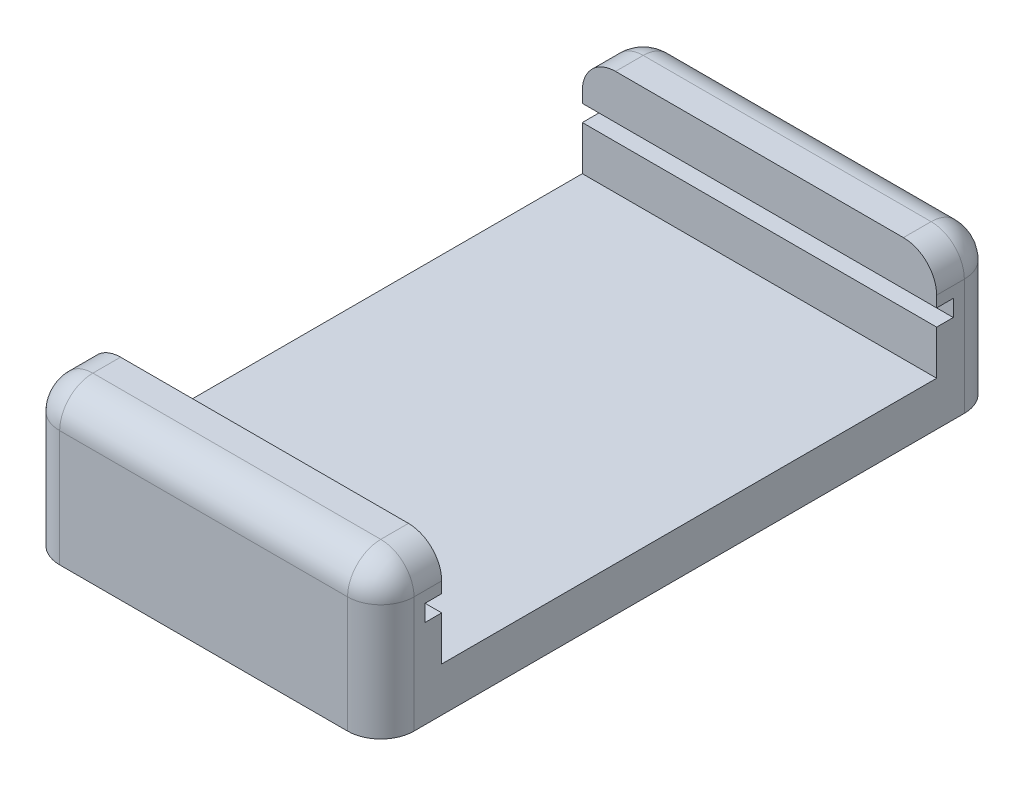
SolidWorks part; units mm, degrees
material "Melamine resin"
ref_plane "Front Plane" through (0, 0, 0) normal (0, 0, 1) x (1, 0, 0)
ref_plane "Top Plane" through (0, 0, 0) normal (0, 1, 0) x (1, 0, 0)
ref_plane "Right Plane" through (0, 0, 0) normal (1, 0, 0) x (0, 0, -1)
sketch "Sketch2" plane through (0, 0, 0) normal (0, 1, 0) x (1, 0, 0)
  line L1 (0, 0) -> (88.9, 0)
  line L2 (0, 0) -> (0, 152.4)
  line L3 (0, 152.4) -> (88.9, 152.4)
  line L10 (88.9, 152.4) -> (88.9, 0)
  dimension "D1" = 152.4
  dimension "D2" = 88.9
extrude "Boss-Extrude1" add sketch "Sketch2" along normal blind 5.9944 contours L3 L10 L1 L2
sketch "Sketch4" plane through (0, 5.9944, 0) normal (0, 1, 0) x (1, 0, 0)
  line L0 (0, 0) -> (0, 152.4) construction
  line L1 (0, 0) -> (88.9, 0) construction
  circle A0 centre (45.72, 109.8713) radius 2.7305
  circle A1 centre (45.72, 33.6713) radius 2.7305
  dimension "D3" = 5.461
  dimension "D4" = 5.461
  dimension "D1" = 76.2
  dimension "D2" = 45.72
  dimension "D5" = 33.6713
extrude "Cut-Extrude2" cut sketch "Sketch4" against normal through all both
ref_plane "Plane1" through (44.45, 0, 0) normal (-1, 0, 0) x (0, 0, 1)
sketch "Sketch6" plane through (44.45, 0, 0) normal (-1, 0, 0) x (0, 0, 1)
  line L0 (0, 5.9944) -> (-152.4, 5.9944) construction
  line L1 (0, 5.9944) -> (-152.4, 5.9944)
  line L3 (-149.86, 5.9944) -> (-79.121, 5.9944)
  line L4 (-149.86, 5.9944) -> (-149.86, 23.1394)
  line L5 (-149.86, 23.1394) -> (-79.121, 23.1394)
  line L6 (-79.121, 5.9944) -> (-79.121, 23.1394)
  line L7 (-142.875, 23.1394) -> (-86.106, 23.1394)
  line L8 (-142.875, 23.1394) -> (-142.875, 11.0744)
  line L9 (-142.875, 11.0744) -> (-86.106, 11.0744)
  line L10 (-86.106, 23.1394) -> (-86.106, 11.0744)
  line L11 (-144.78, 18.0594) -> (-84.201, 18.0594)
  line L12 (-144.78, 18.0594) -> (-144.78, 16.1544)
  line L13 (-144.78, 16.1544) -> (-84.201, 16.1544)
  line L14 (-84.201, 18.0594) -> (-84.201, 16.1544)
  line L15 (-152.4, 5.9944) -> (-152.4, 0) construction
  dimension "D1" = 60.579
  dimension "D2" = 1.905
  dimension "D3" = 1.905
  dimension "D4" = 1.905
  dimension "D5" = 5.08
  dimension "D6" = 5.08
  dimension "D7" = 5.08
  dimension "D8" = 5.08
  dimension "D9" = 5.08
  dimension "D10" = 2.54
extrude "Boss-Extrude3" add sketch "Sketch6" along normal mid plane 40.64 contours L11 L14 L13 L10 L9 L8 L12 L5 L4 L1 L6
fillet "Fillet3" radius 3.81 2 edges at (44.45, 23.1394, -79.121) (44.45, 23.1394, -149.86)
fillet "Fillet6" radius 3.81 12 edges at (24.13, 23.1394, -84.5185) (24.13, 22.0235, -80.2369) (64.77, 23.1394, -84.5185) (64.77, 22.0235, -80.2369) (64.77, 23.1394, -144.4625) (64.77, 22.0235, -148.7441) (24.13, 23.1394, -144.4625) (24.13, 22.0235, -148.7441) (24.13, 12.6619, -79.121) (64.77, 12.6619, -79.121) (64.77, 12.6619, -149.86) (24.13, 12.6619, -149.86)
sketch "Sketch7" plane through (0, 5.9944, 0) normal (0, 1, 0) x (1, 0, 0)
  line L0 (0, 0) -> (88.9, 0) construction
  line L1 (0, 152.4) -> (2.54, 152.4)
  line L2 (0, 152.4) -> (0, 0)
  line L3 (0, 0) -> (2.54, 0)
  line L4 (2.54, 152.4) -> (2.54, 0)
  dimension "D1" = 2.54
extrude "Cut-Extrude3" cut sketch "Sketch7" against normal through all both
sketch "Sketch8" plane through (0, 0, 0) normal (0, -1, 0) x (1, 0, 0)
  line L4 (2.54, 0) -> (2.54, -152.4)
  line L5 (2.54, -152.4) -> (88.9, -152.4)
  line L6 (88.9, -152.4) -> (88.9, 0)
  line L7 (88.9, 0) -> (2.54, 0)
  line L8 (2.54, 0) -> (2.54, -152.4)
  line L9 (2.54, -152.4) -> (88.9, -152.4)
  line L10 (88.9, -152.4) -> (88.9, 0)
  line L11 (88.9, 0) -> (2.54, 0)
  circle A0 centre (45.72, -33.6713) radius 2.7305 construction
  circle A1 centre (45.72, -33.6713) radius 2.7305
  circle A2 centre (45.72, -109.8713) radius 2.7305 construction
  circle A3 centre (45.72, -109.8713) radius 2.7305
  dimension "D1" = 0
extrude "Cut-Extrude5" cut sketch "Sketch8" against normal up to surface (5.9944 mm away) up to face at (45.72, 5.9944, -76.2)
sketch "Sketch9" plane through (0, 5.9944, 0) normal (0, -1, 0) x (1, 0, 0)
  line L0 (44.45, 10.9153) -> (44.45, -10.9153) construction
  line L1 (44.45, -89.0905) -> (44.45, -139.8905) construction
  line L2 (64.77, -82.931) -> (64.77, -146.05) construction
  circle A0 centre (44.45, -89.0905) radius 2.7305
  circle A1 centre (44.45, -139.8905) radius 2.7305
  point P8 (64.77, -114.4905)
  point P9 (44.45, -114.4905)
  dimension "D1" = 5.461
  dimension "D2" = 5.461
  dimension "D3" = 50.8
extrude "Cut-Extrude6" cut sketch "Sketch9" against normal blind 4.064
equation "\"threaded_insert_hole\"=0.1472"
equation "\"th\"=1.25249"
